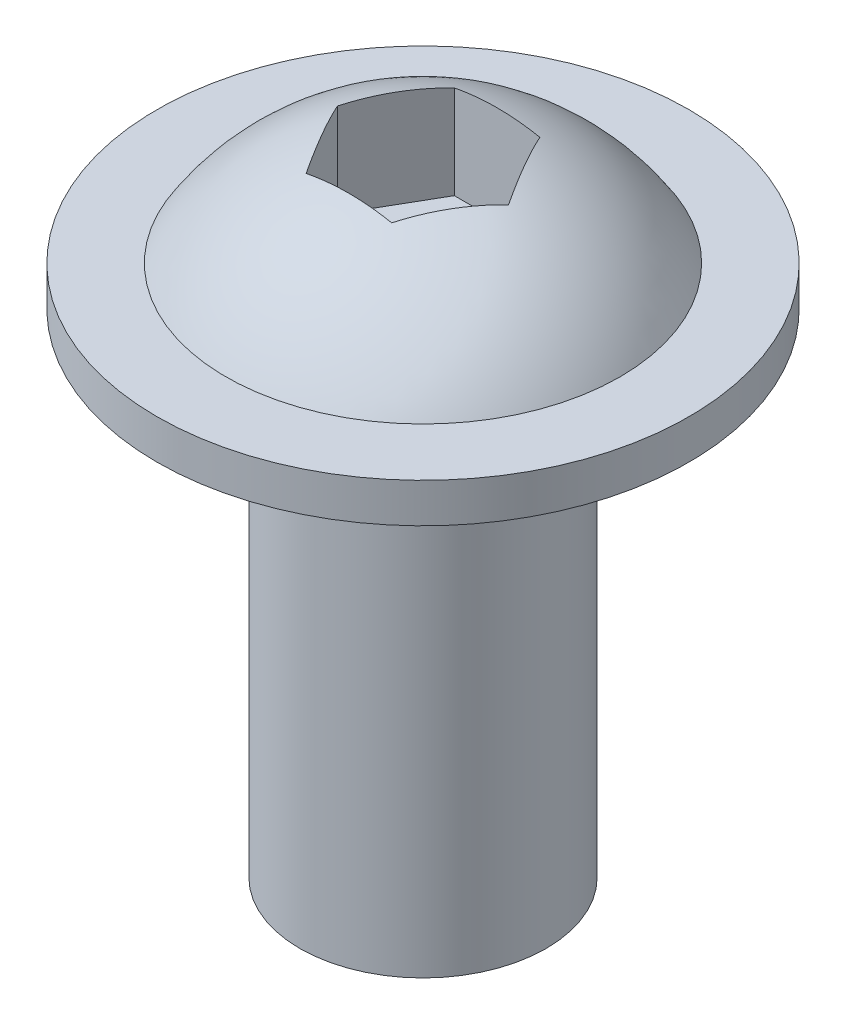
SolidWorks part; units mm, degrees
ref_plane "Front"
ref_plane "Top" through (0, 0, 0) normal (0, 1, 0) x (1, 0, 0)
ref_plane "Right" through (0, 0, 0) normal (1, 0, 0) x (0, 0, -1)
sketch "Sketch1" plane through (0, 0, 0) normal (0, 0, 1) x (1, 0, 0)
  line L0 (0, 0) -> (3.9688, 0)
  line L1 (3.9688, 0) -> (3.9688, 15.875)
  line L2 (3.9688, 15.875) -> (8.5725, 15.875)
  line L3 (8.5725, 15.875) -> (8.5725, 17.145)
  line L4 (8.5725, 17.145) -> (6.35, 17.145)
  line L5 (0, 0) -> (0, 20.32)
  line L6 (0, 0) -> (0, 30.7805) construction
  line L8 (2.2914, 20.32) -> (0, 20.32)
  arc A0 (6.35, 17.145) -> (2.2914, 20.32) centre (0, 13.2093) ccw
  dimension "MajorDia" = 7.9375
  dimension "D2" = 4.5827
  dimension "Length" = 15.875
  dimension "FlangeThick" = 1.27
  dimension "FlangeDiam" = 17.145
  dimension "HeadHeight" = 4.445
  dimension "HeadDiam" = 12.7
revolve "Screw revolve" add sketch "Sketch1" angle 360 about L6
sketch "Sketch2" plane through (0, 20.32, 0) normal (0, 1, 0) x (-1, 0, 0)
  line L1 (-2.757, 0) -> (-1.3785, -2.3876)
  line L2 (-1.3785, -2.3876) -> (1.3785, -2.3876)
  line L3 (1.3785, -2.3876) -> (2.757, 0)
  line L4 (2.757, 0) -> (1.3785, 2.3876)
  line L5 (1.3785, 2.3876) -> (-1.3785, 2.3876)
  line L6 (-1.3785, 2.3876) -> (-2.757, 0)
  circle A0 centre (0, 0) radius 2.3876 construction
  dimension "D1" = 5.5139
  dimension "HexWidth" = 4.7752
extrude "Hex Cut" cut sketch "Sketch2" against normal blind 3.175
equation "\"D2@Sketch1\" = \"D1@Sketch2\""
